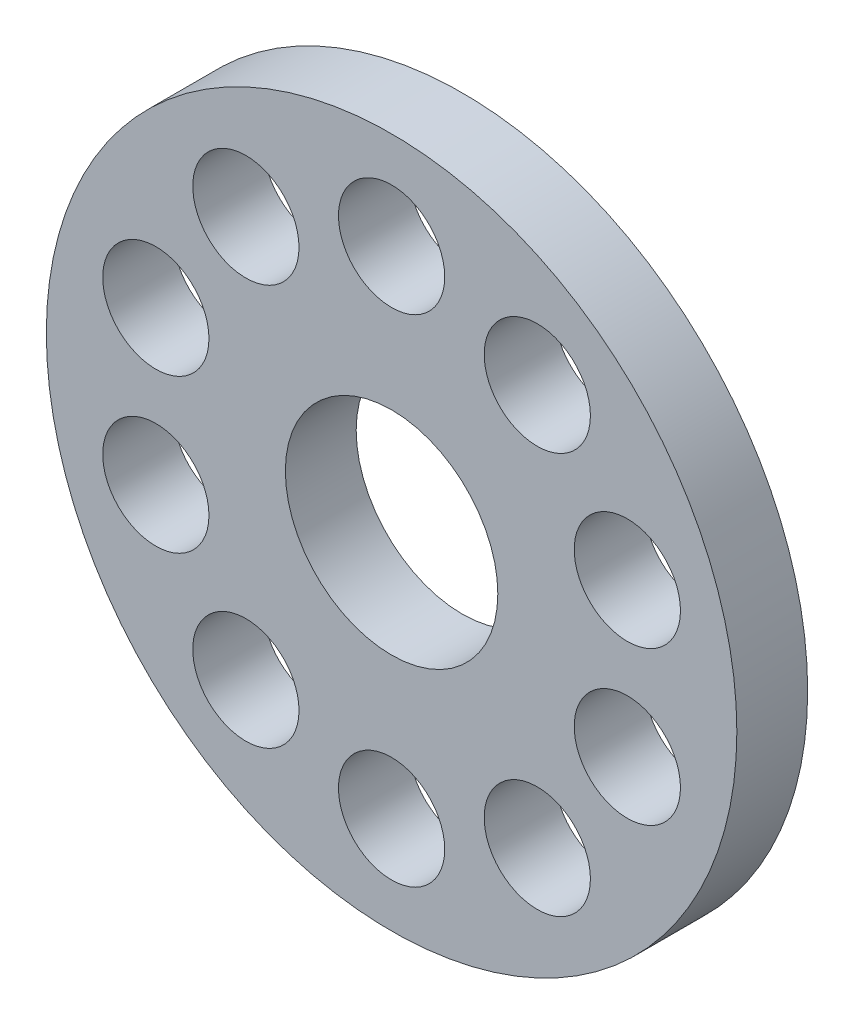
SolidWorks part; units mm, degrees
ref_plane "Front Plane" through (0, 0, 0) normal (0, 0, 1) x (1, 0, 0)
ref_plane "Top Plane" through (0, 0, 0) normal (0, 1, 0) x (1, 0, 0)
ref_plane "Right Plane" through (0, 0, 0) normal (1, 0, 0) x (0, 0, -1)
sketch "Sketch1" plane through (0, 0, 0) normal (0, 0, 1) x (1, 0, 0)
  circle A1 centre (0, 0) radius 3
  circle A2 centre (0, 7) radius 1.5
  circle A3 centre (0, 0) radius 9.75
  circle A4 centre (4.1145, 5.6631) radius 1.5
  circle A5 centre (6.6574, 2.1631) radius 1.5
  circle A6 centre (6.6574, -2.1631) radius 1.5
  circle A7 centre (4.1145, -5.6631) radius 1.5
  circle A8 centre (0, -7) radius 1.5
  circle A9 centre (-4.1145, -5.6631) radius 1.5
  circle A10 centre (-6.6574, -2.1631) radius 1.5
  circle A11 centre (-6.6574, 2.1631) radius 1.5
  circle A12 centre (-4.1145, 5.6631) radius 1.5
  dimension "D2" = 10
extrude "Boss-Extrude1" add sketch "Sketch1" against normal blind 2
